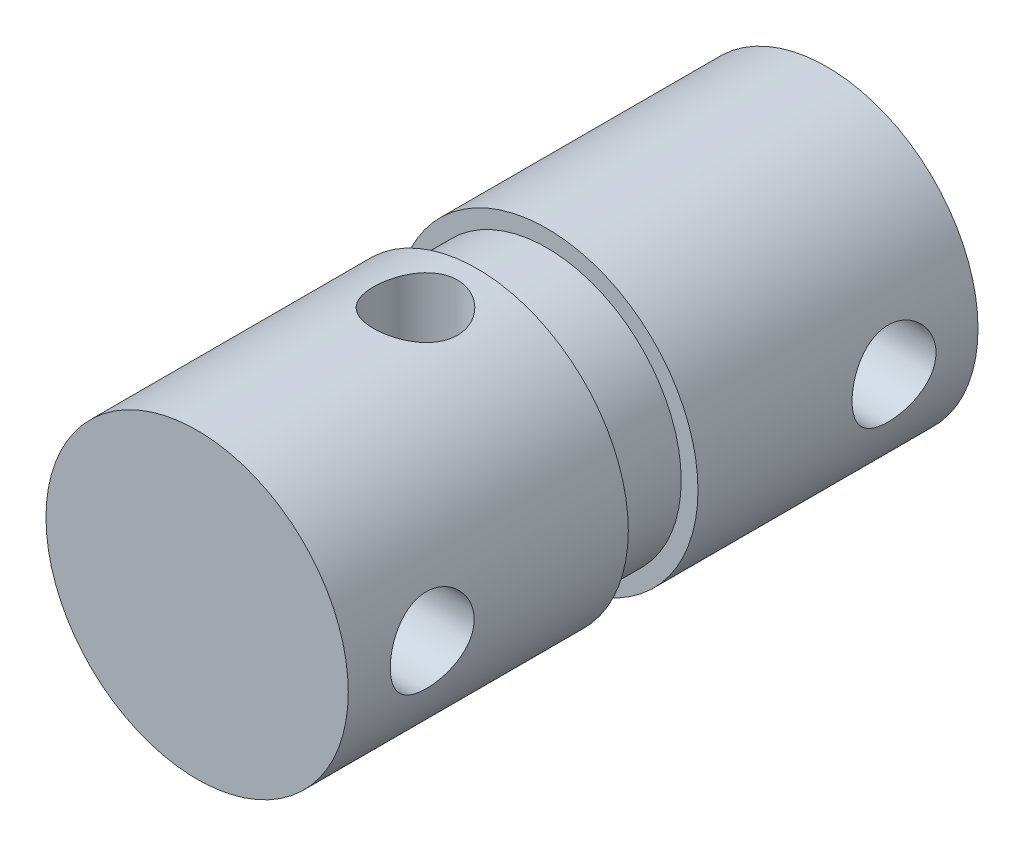
SolidWorks part; units mm, degrees
ref_plane "Front Plane" through (0, 0, 0) normal (0, 0, 1) x (1, 0, 0)
ref_plane "Top Plane" through (0, 0, 0) normal (0, 1, 0) x (1, 0, 0)
ref_plane "Right Plane" through (0, 0, 0) normal (1, 0, 0) x (0, 0, -1)
sketch "Sketch2" plane through (0, 0, 0) normal (0, 1, 0) x (1, 0, 0)
  line L0 (0, 0) -> (0, -19.05)
  line L1 (0, -19.05) -> (4.572, -19.05)
  line L2 (4.572, -19.05) -> (4.572, -10.5791)
  line L3 (4.572, -10.5791) -> (4.064, -10.5791)
  line L4 (4.064, -10.5791) -> (4.064, -8.4709)
  line L5 (4.064, -8.4709) -> (4.572, -8.4709)
  line L6 (4.572, -8.4709) -> (4.572, 0)
  line L7 (4.572, 0) -> (0, 0)
  line L8 (0, -9.525) -> (4.064, -9.525) construction
  point P11 (4.064, -9.525)
  dimension "D1" = 19.05
  dimension "D2" = 4.572
  dimension "D3" = 2.1082
  dimension "D4" = 0.508
revolve "Revolve1" add sketch "Sketch2" angle 360 about L0
sketch "Sketch3" plane through (0, 0, 0) normal (0, 1, 0) x (1, 0, 0)
  line L0 (-4.572, -19.05) -> (4.572, -19.05) construction
  line L1 (0, -19.05) -> (0, -12.446) construction
  circle A0 centre (0, -12.446) radius 1.27
  point P2 (0, -13.716)
  dimension "D1" = 2.54
  dimension "D2" = 5.334
extrude "Cut-Extrude1" cut sketch "Sketch3" against normal through all both and the other way through all
sketch "Sketch4" plane through (0, 0, 0) normal (1, 0, 0) x (0, 0, -1)
  line L0 (0, 0) -> (-2.54, 0) construction
  line L1 (-9.525, 4.064) -> (-9.525, -4.064) construction
  line L2 (-8.4709, 4.064) -> (-10.5791, 4.064) construction
  line L3 (-10.5791, -4.064) -> (-8.4709, -4.064) construction
  circle A0 centre (-2.54, 0) radius 1.27
  circle A1 centre (-16.51, 0) radius 1.27
  point P3 (-1.27, 0)
  dimension "D1" = 2.54
  dimension "D2" = 1.27
extrude "Cut-Extrude2" cut sketch "Sketch4" against normal through all both and the other way through all contours A0 | A1
